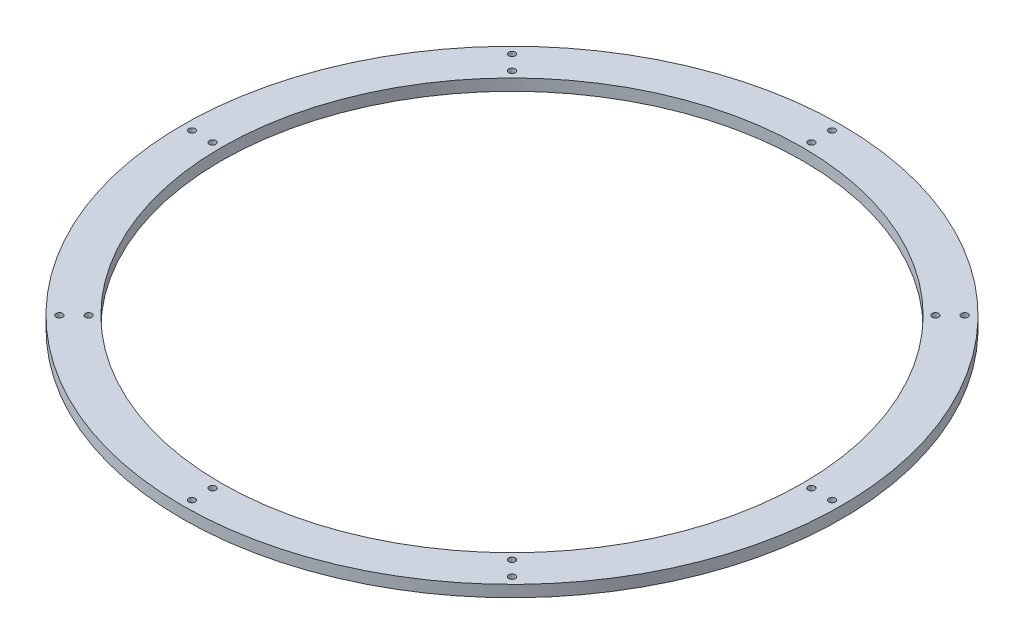
SolidWorks part; units mm, degrees
ref_plane "Front Plane" through (0, 0, 0) normal (0, 0, 1) x (1, 0, 0)
ref_plane "Top Plane" through (0, 0, 0) normal (0, 1, 0) x (1, 0, 0)
ref_plane "Right Plane" through (0, 0, 0) normal (1, 0, 0) x (0, 0, -1)
sketch "Sketch1" plane through (0, 0, 0) normal (0, 1, 0) x (1, 0, 0)
  circle A0 centre (0, 0) radius 399
extrude "Boss-Extrude1" add sketch "Sketch1" along normal blind 14
sketch "Sketch2" plane through (0, 14, 0) normal (0, 1, 0) x (1, 0, 0)
  circle A0 centre (0, 0) radius 352
extrude "Cut-Extrude1" cut sketch "Sketch2" against normal blind 14
sketch "Sketch3" plane through (0, 14, 0) normal (0, 1, 0) x (1, 0, 0)
  line L0 (0, 0) -> (0, 387.5)
  circle A0 centre (0, 0) radius 375.5
  circle A1 centre (0, 0) radius 387.5
sketch "Sketch4" plane through (0, 0, 0) normal (0, -1, 0) x (-1, 0, 0)
  circle A0 centre (0, 387.5) radius 4
extrude "Cut-Extrude2" cut sketch "Sketch4" against normal blind 19.304
sketch "Sketch5" plane through (0, 0, 0) normal (1, 0, 0) x (0, 0, -1)
  line L0 (0, -1.5898) -> (0, 98.5765)
pattern_circular "CirPattern1" count 8 over 360 about axis through (0, 0, 0) along (0, 1, 0) of "Cut-Extrude2"
sketch "Sketch6" plane through (0, 0, 0) normal (0, -1, 0) x (1, 0, 0)
  circle A0 centre (0, 0) radius 362.5
sketch "Sketch7" plane through (0, 14, 0) normal (0, 1, 0) x (1, 0, 0)
  circle A0 centre (0, 362.5) radius 4
extrude "Cut-Extrude3" cut sketch "Sketch7" against normal through all
pattern_circular "CirPattern2" count 8 over 360 about axis through (0, 0, 0) along (0, 1, 0) of "Cut-Extrude3"
